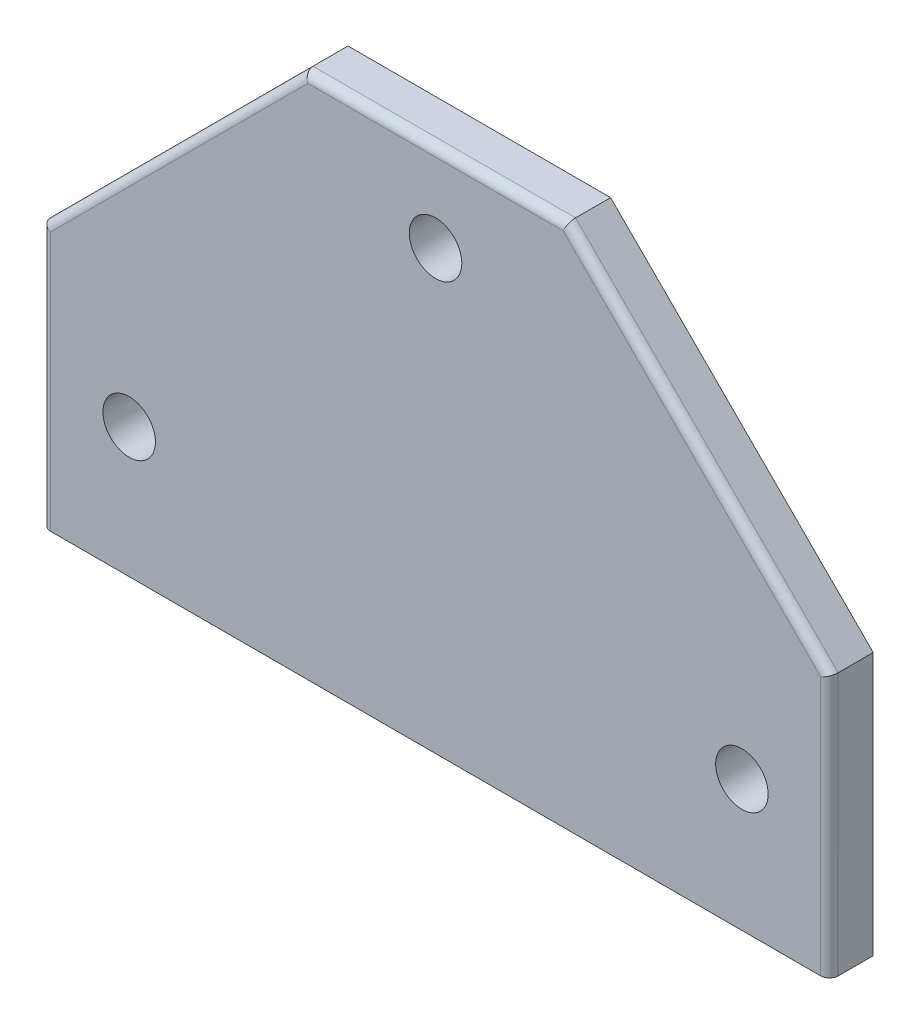
SolidWorks part; units mm, degrees
ref_plane "Front Plane" through (0, 0, 0) normal (0, 0, 1) x (1, 0, 0)
ref_plane "Top Plane" through (0, 0, 0) normal (0, 1, 0) x (1, 0, 0)
ref_plane "Right Plane" through (0, 0, 0) normal (1, 0, 0) x (0, 0, -1)
sketch "Sketch1" plane through (0, 0, 0) normal (0, 0, 1) x (1, 0, 0)
  line L0 (0, 38.1) -> (38.1, 76.2)
  line L1 (0, 0) -> (114.3, 0)
  line L2 (0, 0) -> (0, 38.1)
  line L4 (114.3, 0) -> (114.3, 38.1)
  line L7 (38.1, 76.2) -> (76.2, 76.2)
  line L10 (76.2, 76.2) -> (114.3, 38.1)
  dimension "D1" = 114.3
  dimension "D2" = 38.1
  dimension "D3" = 38.1
  dimension "D4" = 38.1
  dimension "D5" = 38.1
  dimension "D6" = 76.2
extrude "Boss-Extrude1" add sketch "Sketch1" along normal blind 6.35
fillet "Fillet1" radius 1.27 5 edges at (114.3, 19.05, 6.35) (95.25, 57.15, 6.35) (0, 19.05, 6.35) (19.05, 57.15, 6.35) (57.15, 76.2, 6.35)
sketch "Sketch3" plane through (0, 0, 6.35) normal (0, 0, 1) x (1, 0, 0)
  line L0 (57.15, 74.93) -> (57.15, 0) construction
  line L1 (75.6739, 74.93) -> (38.6261, 74.93) construction
  line L2 (1.27, 0) -> (113.03, 0) construction
  line L3 (1.27, 18.787) -> (114.3, 19.05) construction
  line L4 (1.27, 37.5739) -> (1.27, 0) construction
  line L5 (114.3, 38.1) -> (114.3, 0) construction
  line L6 (38.1, 76.2) -> (76.2, 76.2) construction
  line L7 (0, 0) -> (0, 38.1) construction
  circle A0 centre (12.7, 18.8136) radius 3.81
  circle A1 centre (101.6, 19.0204) radius 3.81
  circle A2 centre (57.15, 63.5) radius 3.81
  dimension "D1" = 7.62
  dimension "D2" = 7.62
  dimension "D3" = 7.62
  dimension "D5" = 12.7
  dimension "D6" = 12.7
  dimension "D4" = 12.7
extrude "Cut-Extrude1" cut sketch "Sketch3" against normal up to surface (6.35 mm away) up to face at (57.15, 38.1, 0)
